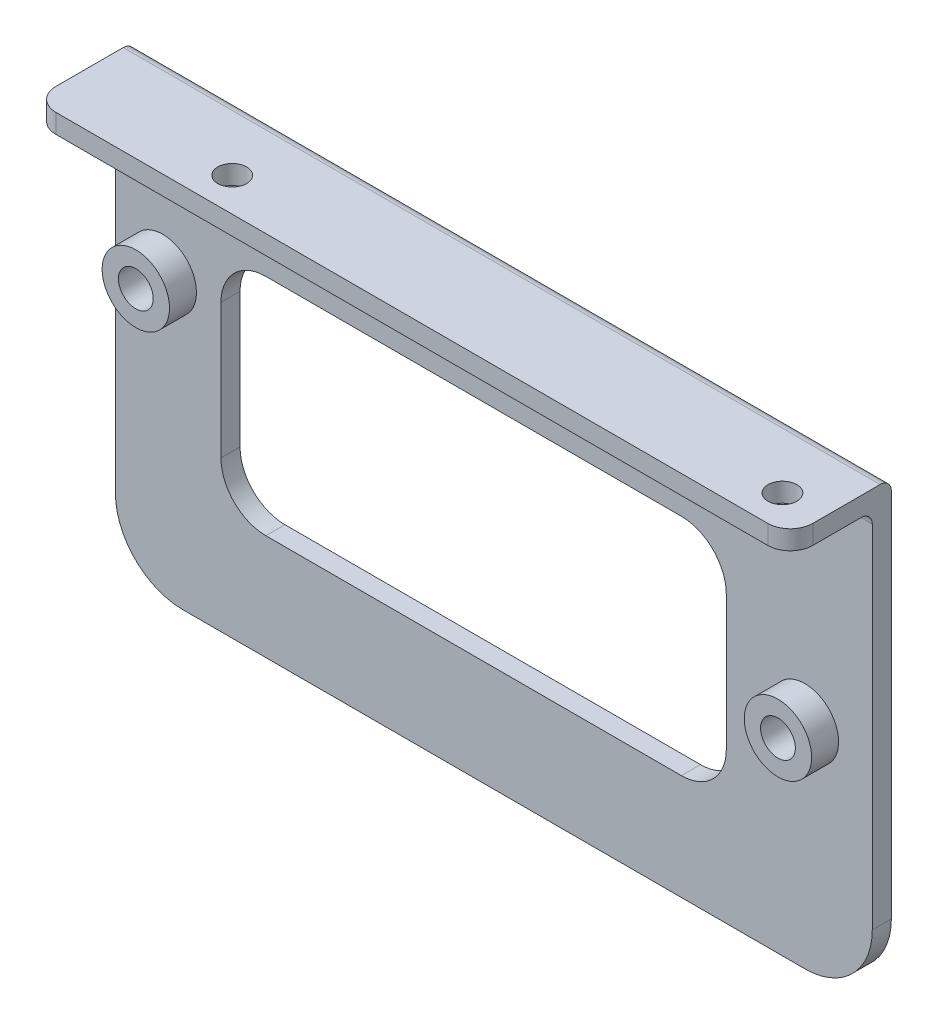
SolidWorks part; units mm, degrees
ref_plane "Front Plane" through (0, 0, 0) normal (0, 0, 1) x (1, 0, 0)
ref_plane "Top Plane" through (0, 0, 0) normal (0, 1, 0) x (1, 0, 0)
ref_plane "Right Plane" through (0, 0, 0) normal (1, 0, 0) x (0, 0, -1)
sketch "Sketch1" plane through (0, 0, 0) normal (0, 0, 1) x (1, 0, 0)
  line L1 (42.799, 25.4) -> (-42.799, 25.4)
  line L2 (42.799, 25.4) -> (42.799, -25.4)
  line L3 (42.799, -25.4) -> (-42.799, -25.4)
  line L4 (-42.799, 25.4) -> (-42.799, -25.4)
  line L5 (42.799, 25.4) -> (-42.799, -25.4) construction
  line L6 (42.799, -25.4) -> (-42.799, 25.4) construction
  point P0 (0, 0)
  dimension "D1" = 85.598
  dimension "D2" = 50.8
extrude "Boss-Extrude1" add sketch "Sketch1" along normal blind 2.159
sketch "Sketch2" plane through (0, 0, 2.159) normal (0, 0, 1) x (1, 0, 0)
  line L0 (-42.799, 25.4) -> (-42.799, -25.4) construction
  line L1 (42.799, 25.4) -> (-42.799, 25.4)
  line L2 (42.799, 25.4) -> (42.799, 23.241)
  line L3 (42.799, 23.241) -> (-42.799, 23.241)
  line L4 (-42.799, 25.4) -> (-42.799, 23.241)
  dimension "D1" = 2.159
extrude "Boss-Extrude2" add sketch "Sketch2" along normal blind 9.271
fillet "Fillet1" radius 1.27 1 edges at (0, 23.241, 2.159)
fillet "Fillet2" radius 1.27 1 edges at (0, 25.4, 0)
fillet "Fillet3" radius 2.54 2 edges at (42.799, 24.3205, 11.43) (-42.799, 24.3205, 11.43)
fillet "Fillet4" radius 7.62 2 edges at (-42.799, -25.4, 1.0795) (42.799, -25.4, 1.0795)
sketch "Sketch3" plane through (0, 0, 2.159) normal (0, 0, 1) x (1, 0, 0)
  line L0 (-35.179, -25.4) -> (35.179, -25.4) construction
  line L1 (-30.861, -13.462) -> (26.289, -13.462)
  line L2 (-30.861, -13.462) -> (-30.861, 11.938)
  line L3 (-30.861, 11.938) -> (26.289, 11.938)
  line L4 (26.289, -13.462) -> (26.289, 11.938)
  line L5 (-42.799, 21.971) -> (-42.799, -17.78) construction
  dimension "D1" = 11.938
  dimension "D2" = 11.938
  dimension "D3" = 25.4
  dimension "D4" = 57.15
extrude "Cut-Extrude1" cut sketch "Sketch3" against normal through all
fillet "Fillet5" radius 5.08 4 edges at (26.289, -13.462, 1.0795) (-30.861, -13.462, 1.0795) (26.289, 11.938, 1.0795) (-30.861, 11.938, 1.0795)
hole_wizard "#4 Clearance Hole1" positions "Sketch4" profile "Sketch5" hole size "#4" standard "ANSI Inch" end condition through all
sketch "Sketch4" plane through (0, 23.241, 0) normal (0, -1, 0) x (-1, 0, 0)
  line L0 (-42.799, -8.89) -> (-42.799, -3.429) construction
  line L1 (40.259, -11.43) -> (-40.259, -11.43) construction
  point P0 (-38.1, -7.62)
  point P2 (24.13, -7.62)
  dimension "D1" = 62.23
  dimension "D2" = 4.699
  dimension "D3" = 3.81
sketch "Sketch5" plane through (38.1, 23.241, 7.62) normal (1, 0, 0) x (0, 0, -1)
  line L0 (0, 0) -> (0, 2.159)
  line L1 (0, 2.159) -> (1.6319, 2.159)
  line L2 (1.6319, 2.159) -> (1.6319, 0)
  line L5 (1.6319, 0) -> (0, 0)
  line L11 (0, -6.35) -> (0, 107.95) construction
  dimension "Thru Hole Dia." = 3.2639
  dimension "Thru Hole Depth" = 2.159
sketch "Sketch6" plane through (0, 0, 2.159) normal (0, 0, 1) x (1, 0, 0)
  line L0 (42.799, -17.78) -> (42.799, 21.971) construction
  line L1 (-35.179, -25.4) -> (35.179, -25.4) construction
  circle A0 centre (35.179, -1.27) radius 3.81
  circle A2 centre (-37.4421, 6.4262) radius 3.81
  dimension "D1" = 7.62
  dimension "D2" = 7.62
  dimension "D4" = 72.6211
  dimension "D3" = 24.13
  dimension "D5" = 7.6962
extrude "Boss-Extrude3" add sketch "Sketch6" along normal blind 3.048
sketch "Sketch8" plane through (0, 0, 5.207) normal (0, 0, 1) x (1, 0, 0)
  circle A0 centre (-37.4421, 6.4262) radius 1.9685
  circle A1 centre (35.179, -1.27) radius 1.9685
  dimension "D1" = 3.937
extrude "Cut-Extrude2" cut sketch "Sketch8" against normal blind 3.429
sketch "Sketch9" plane through (0, 0, 1.778) normal (0, 0, 1) x (1, 0, 0)
  circle A0 centre (-37.4421, 6.4262) radius 0.9525
  circle A1 centre (35.179, -1.27) radius 0.9525
  dimension "D1" = 1.905
extrude "Cut-Extrude3" cut sketch "Sketch9" against normal through all
